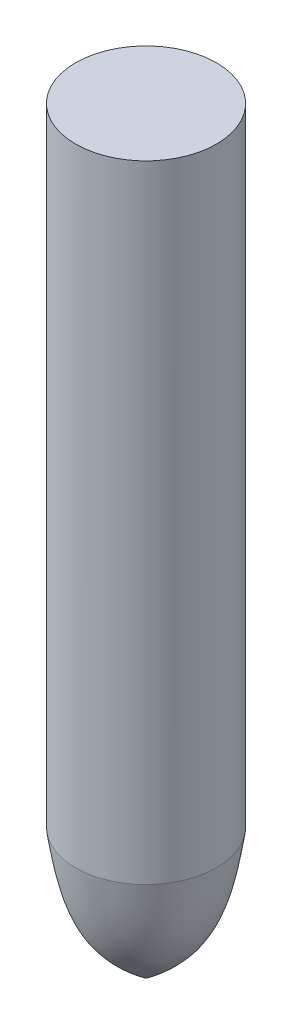
SolidWorks part; units mm, degrees
ref_plane "Front Plane" through (0, 0, 0) normal (0, 0, 1) x (1, 0, 0)
ref_plane "Top Plane" through (0, 0, 0) normal (0, 1, 0) x (1, 0, 0)
ref_plane "Right Plane" through (0, 0, 0) normal (1, 0, 0) x (0, 0, -1)
sketch "Sketch1" plane through (0, 0, 0) normal (0, 1, 0) x (1, 0, 0)
  circle A0 centre (0, 0) radius 70
  dimension "D1" = 140
extrude "Extrude1" add sketch "Sketch1" along normal mid plane 750
sketch "Sketch2" plane through (0, 0, 0) normal (0, 0, 1) x (1, 0, 0)
  line L0 (-70, 375) -> (-70, -375) construction
  line L1 (-70, -247.7943) -> (-139.1287, -247.7943)
  line L2 (-139.1287, -247.7943) -> (-117.3494, -403.9204)
  line L3 (-117.3494, -403.9204) -> (0, -421.3796)
  line L4 (0, -421.3796) -> (0, -377.9712)
  line L5 (0, -315.5502) -> (0, -141.7192) construction
  spline S0 degree 3 poles (0, -377.9712) (-15.7691, -365.4724) (-56.7537, -332.9875) (-64.9545, -280.2442) (-70, -247.7943) knots 0 0 0 0 0.384757 1 1 1 1
revolve "Cut-Revolve1" cut sketch "Sketch2" angle 360 about L5
